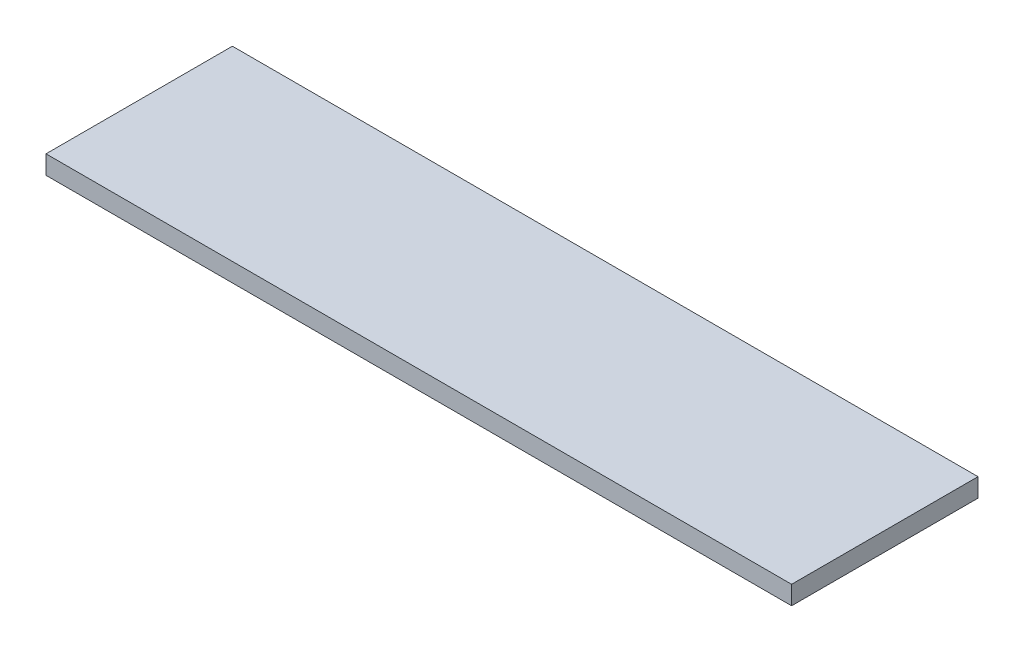
SolidWorks part; units mm, degrees
ref_plane "Face" through (0, 0, 0) normal (0, 0, 1) x (1, 0, 0)
ref_plane "Dessus" through (0, 0, 0) normal (0, 1, 0) x (1, 0, 0)
ref_plane "Droite" through (0, 0, 0) normal (1, 0, 0) x (0, 0, -1)
sketch "Esquisse1" plane through (0, 0, 0) normal (0, 1, 0) x (1, 0, 0)
  line L1 (0, 0) -> (200, 0)
  line L2 (0, 0) -> (0, 50)
  line L3 (0, 50) -> (200, 50)
  line L4 (200, 0) -> (200, 50)
  dimension "D1" = 50
  dimension "D2" = 200
extrude "Extrusion1" add sketch "Esquisse1" along normal blind 5
